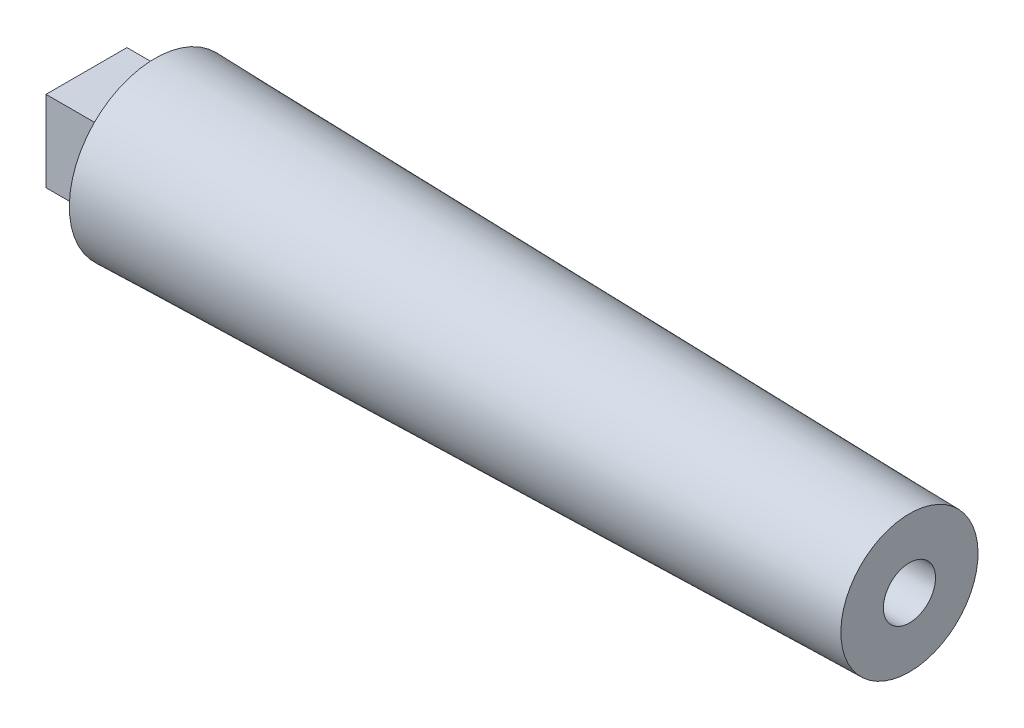
SolidWorks part; units mm, degrees
ref_plane "Front Plane" through (0, 0, 0) normal (0, 0, 1) x (1, 0, 0)
ref_plane "Top Plane" through (0, 0, 0) normal (0, 1, 0) x (1, 0, 0)
ref_plane "Right Plane" through (0, 0, 0) normal (1, 0, 0) x (0, 0, -1)
sketch "Sketch1" plane through (0, 0, 0) normal (0, 0, 1) x (1, 0, 0)
  line L0 (12.7, 0) -> (59.4829, 0) construction
  line L3 (12.7, 12.7) -> (12.7, 15.875)
  line L4 (12.7, 15.875) -> (152.4, 12.7)
  line L5 (152.4, 12.7) -> (152.4, 0)
  line L6 (12.7, 0) -> (152.4, 0)
  line L7 (12.7, 12.7) -> (12.7, 0)
  dimension "D2" = 31.75
  dimension "D3" = 25.4
revolve "Revolve1" add sketch "Sketch1" angle 360 about L0
sketch "Sketch2" plane through (152.4, 0, 0) normal (1, 0, 0) x (0, 0, -1)
  circle A0 centre (0, 0) radius 4.826
  dimension "D1" = 9.652
extrude "Cut-Extrude1" cut sketch "Sketch2" against normal blind 25.4
sketch "Sketch3" plane through (12.7, 0, 0) normal (-1, 0, 0) x (0, 0, 1)
  line L1 (7.493, -7.493) -> (-7.493, -7.493)
  line L2 (7.493, -7.493) -> (7.493, 7.493)
  line L3 (7.493, 7.493) -> (-7.493, 7.493)
  line L4 (-7.493, -7.493) -> (-7.493, 7.493)
  line L5 (7.493, -7.493) -> (-7.493, 7.493) construction
  line L6 (7.493, 7.493) -> (-7.493, -7.493) construction
  point P0 (0, 0)
  dimension "D1" = 14.986
extrude "Boss-Extrude1" add sketch "Sketch3" along normal blind 12.7
